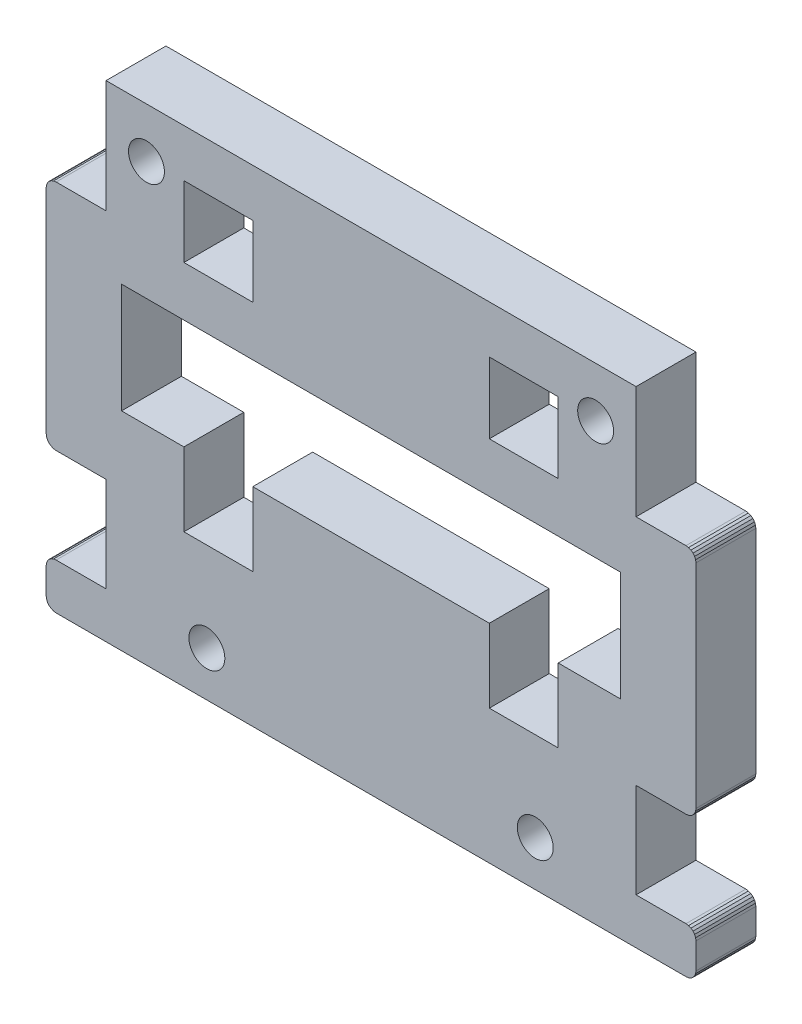
SolidWorks part; units mm, degrees
ref_plane "Plano frontal" through (0, 0, 0) normal (0, 0, 1) x (1, 0, 0)
ref_plane "Plano superior" through (0, 0, 0) normal (0, 1, 0) x (1, 0, 0)
ref_plane "Plano direito" through (0, 0, 0) normal (1, 0, 0) x (0, 0, -1)
sketch "Model" plane through (0, 0, 0) normal (0, 0, 1) x (1, 0, 0)
  line L0 (98.0343, 10.6121) -> (98.1342, 10.371)
  line L1 (97.8754, 20.9036) -> (98.0343, 21.1107)
  line L2 (98.0343, 21.1107) -> (98.1342, 21.3519)
  line L3 (84.3683, 50.4282) -> (84.3683, 43.3282)
  line L4 (53.7683, 27.3282) -> (53.7683, 19.9597)
  line L5 (33.3612, 20.9036) -> (33.2022, 21.1107)
  line L6 (97.8754, 10.8192) -> (98.0343, 10.6121)
  line L7 (98.1342, 43.1695) -> (98.1683, 42.9107)
  line L8 (33.8094, 43.8766) -> (33.5683, 43.7767)
  line L9 (40.6183, 27.3282) -> (46.8683, 27.3282)
  line L10 (53.7683, 27.3282) -> (77.4683, 27.3282)
  line L11 (84.3683, 27.3282) -> (84.3683, 19.9597)
  line L12 (77.4683, 50.4282) -> (84.3683, 50.4282)
  line L13 (34.0683, 20.6107) -> (39.0683, 20.6107)
  line L14 (33.1023, 7.2577) -> (33.0683, 7.5164)
  line L15 (33.8094, 20.6448) -> (33.5683, 20.7447)
  line L16 (33.5683, 20.7447) -> (33.3612, 20.9036)
  line L17 (46.8683, 19.9597) -> (46.8683, 27.3282)
  line L18 (77.4683, 43.3282) -> (77.4683, 50.4282)
  line L19 (40.6183, 38.3282) -> (40.6183, 27.3282)
  line L20 (39.0683, 43.9107) -> (34.0683, 43.9107)
  line L21 (97.8754, 6.8053) -> (97.6683, 6.6464)
  line L22 (97.6683, 6.6464) -> (97.4271, 6.5465)
  line L23 (97.1683, 11.1121) -> (92.1683, 11.1121)
  line L24 (97.4271, 6.5465) -> (97.1683, 6.5124)
  line L25 (97.1683, 11.1121) -> (97.4271, 11.0781)
  line L26 (97.4271, 11.0781) -> (97.6683, 10.9782)
  line L27 (92.1683, 20.6107) -> (97.1683, 20.6107)
  line L28 (34.0675, 6.5164) -> (33.8088, 6.5506)
  line L29 (33.8088, 6.5506) -> (33.5678, 6.6506)
  line L30 (33.5678, 6.6506) -> (33.3609, 6.8095)
  line L31 (33.5683, 43.7767) -> (33.3612, 43.6178)
  line L32 (33.3612, 43.6178) -> (33.2022, 43.4107)
  line L33 (33.2022, 43.4107) -> (33.1023, 43.1695)
  line L34 (33.0683, 42.9107) -> (33.0683, 21.6107)
  line L35 (33.1023, 43.1695) -> (33.0683, 42.9107)
  line L36 (98.1683, 7.5124) -> (98.1683, 10.1121)
  line L37 (77.4683, 19.9597) -> (77.4683, 27.3282)
  line L38 (33.2022, 10.6107) -> (33.1023, 10.3695)
  line L39 (33.0683, 10.1107) -> (33.0683, 7.5164)
  line L40 (33.1023, 10.3695) -> (33.0683, 10.1107)
  line L41 (97.1683, 20.6107) -> (97.4271, 20.6448)
  line L42 (97.4271, 20.6448) -> (97.6683, 20.7447)
  line L43 (97.6683, 20.7447) -> (97.8754, 20.9036)
  line L44 (34.0683, 43.9107) -> (33.8094, 43.8766)
  line L45 (97.1683, 43.9107) -> (97.4271, 43.8766)
  line L46 (97.4271, 43.8766) -> (97.6683, 43.7767)
  line L47 (97.6683, 43.7767) -> (97.8754, 43.6178)
  line L48 (97.8754, 43.6178) -> (98.0343, 43.4107)
  line L49 (98.0343, 43.4107) -> (98.1342, 43.1695)
  line L50 (98.1342, 10.371) -> (98.1683, 10.1121)
  line L51 (33.2022, 21.1107) -> (33.1023, 21.3519)
  line L52 (33.1023, 21.3519) -> (33.0683, 21.6107)
  line L53 (34.0683, 11.1107) -> (33.8094, 11.0766)
  line L54 (33.8094, 11.0766) -> (33.5683, 10.9767)
  line L55 (33.5683, 10.9767) -> (33.3612, 10.8178)
  line L56 (33.3612, 10.8178) -> (33.2022, 10.6107)
  line L57 (98.1683, 21.6107) -> (98.1683, 42.9107)
  line L58 (98.1342, 21.3519) -> (98.1683, 21.6107)
  line L59 (97.6683, 10.9782) -> (97.8754, 10.8192)
  line L60 (98.1683, 7.5124) -> (98.1342, 7.2536)
  line L61 (98.1342, 7.2536) -> (98.0343, 7.0124)
  line L62 (98.0343, 7.0124) -> (97.8754, 6.8053)
  line L63 (92.1683, 55.2107) -> (92.1683, 43.9107)
  line L64 (90.6183, 38.3282) -> (40.6183, 38.3282)
  line L65 (53.7683, 19.9597) -> (46.8683, 19.9597)
  line L66 (46.8683, 43.3282) -> (46.8683, 50.4282)
  line L67 (53.7683, 43.3282) -> (46.8683, 43.3282)
  line L68 (53.7683, 50.4282) -> (53.7683, 43.3282)
  line L69 (33.3609, 6.8095) -> (33.2021, 7.0166)
  line L70 (33.2021, 7.0166) -> (33.1023, 7.2577)
  line L71 (34.0683, 20.6107) -> (33.8094, 20.6448)
  line L72 (92.1683, 55.2107) -> (39.0683, 55.2107)
  line L73 (92.1683, 11.1121) -> (92.1683, 20.6107)
  line L74 (46.8683, 50.4282) -> (53.7683, 50.4282)
  line L75 (39.0683, 11.1107) -> (39.0683, 20.6107)
  line L76 (39.0683, 55.2107) -> (39.0683, 43.9107)
  line L77 (92.1683, 43.9107) -> (97.1683, 43.9107)
  line L78 (39.0683, 11.1107) -> (34.0683, 11.1107)
  line L79 (84.3683, 27.3282) -> (90.6183, 27.3282)
  line L80 (90.6183, 27.3282) -> (90.6183, 38.3282)
  line L81 (84.3683, 43.3282) -> (77.4683, 43.3282)
  line L82 (84.3683, 19.9597) -> (77.4683, 19.9597)
  line L83 (34.0675, 6.5164) -> (97.1683, 6.5124)
  circle A0 centre (49.1683, 11.0282) radius 1.8
  circle A1 centre (82.0683, 11.0282) radius 1.8
  circle A2 centre (88.1183, 50.2107) radius 1.8
  circle A3 centre (43.1183, 50.2107) radius 1.8
extrude "Ressalto-extrusão1" add sketch "Model" along normal blind 6
ref_plane "Plano1" through (65.6183, 0, 0) normal (1, 0, 0) x (0, 0, -1)
ref_plane "Plano2" through (0, 35.1939, 0) normal (0, 1, 0) x (1, 0, 0)
